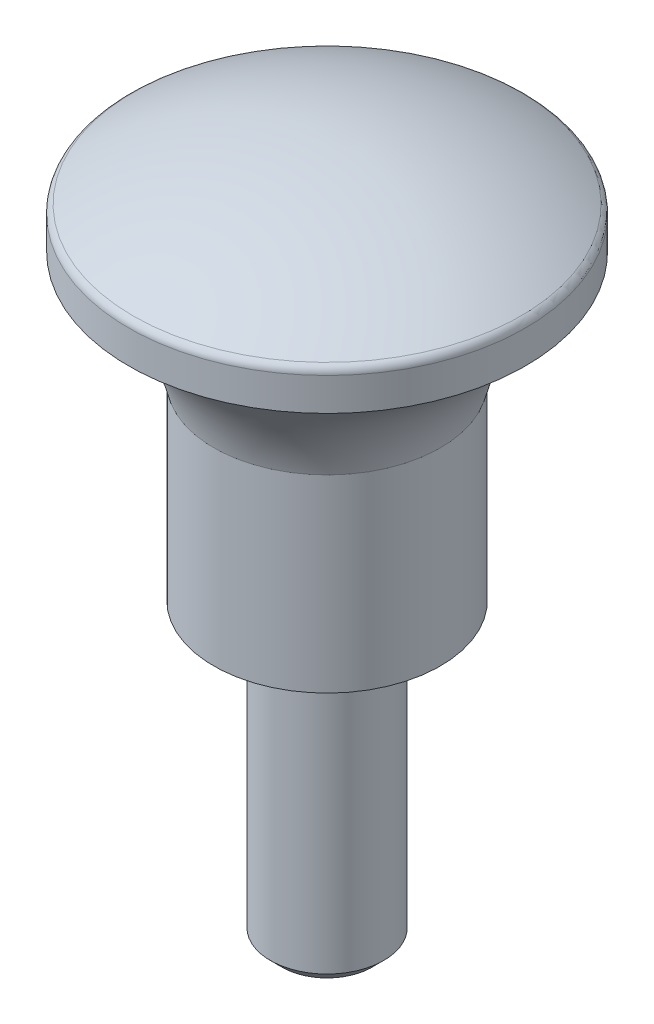
SolidWorks part; units mm, degrees
ref_plane "Plan de face" through (0, 0, 0) normal (0, 0, 1) x (1, 0, 0)
ref_plane "Plan de dessus" through (0, 0, 0) normal (0, 1, 0) x (1, 0, 0)
ref_plane "Plan de droite" through (0, 0, 0) normal (1, 0, 0) x (0, 0, -1)
sketch "Esquisse1" plane through (0, 0, 0) normal (1, 0, 0) x (0, 0, -1)
  line L0 (10.5, 23.3541) -> (10.5, 21.6134)
  line L1 (6, 15.6134) -> (6, 5.6134)
  line L2 (6, 5.6134) -> (3, 5.6134)
  line L3 (3, 5.6134) -> (3, -9.3866)
  line L4 (3, -9.3866) -> (2.3866, -10)
  line L5 (2.3866, -10) -> (0, -10)
  line L6 (0, -10) -> (0, 26.6134)
  line L7 (0, -10) -> (0, 26.6134) construction
  arc A0 (0, 26.6134) -> (10.2564, 23.7834) centre (0, 6.6134) cw
  arc A1 (10.2564, 23.7834) -> (10.5, 23.3541) centre (10, 23.3541) cw
  arc A2 (10.5, 21.6134) -> (6, 15.6134) centre (14.7952, 13.7045) ccw
  dimension "D1" = 15
  dimension "D2" = 10
revolve "Révolution1" add sketch "Esquisse1" angle 360 about L7
